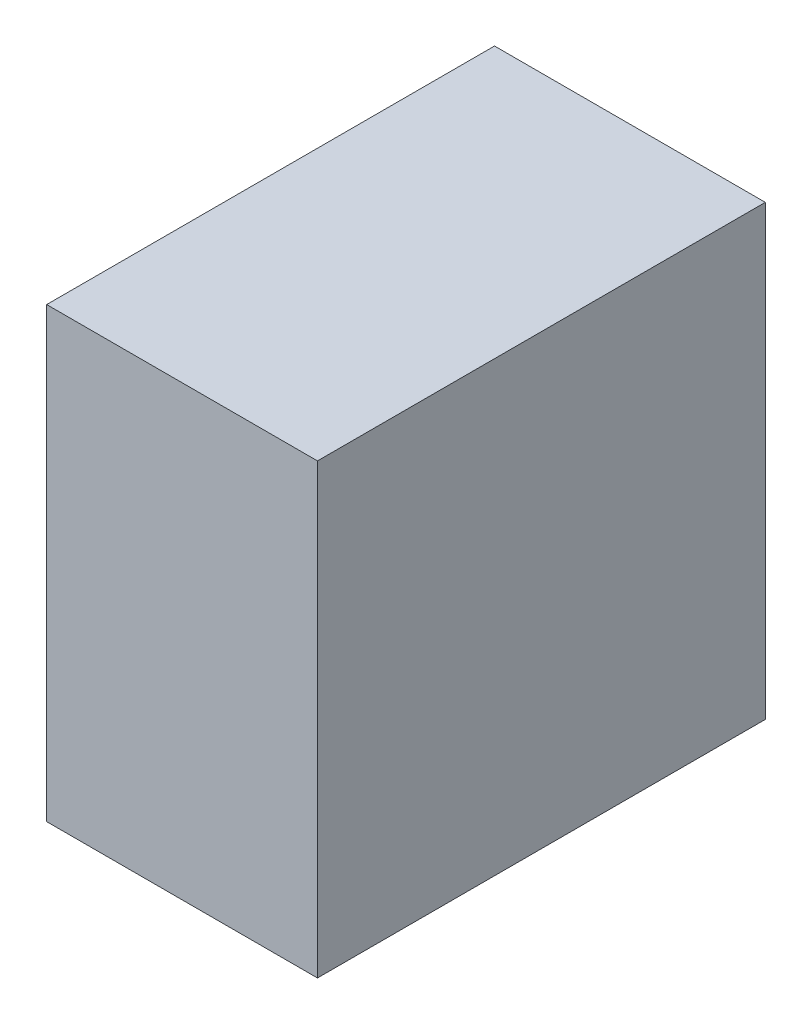
SolidWorks part; units mm, degrees
ref_plane "Ön Düzlem" through (0, 0, 0) normal (0, 0, 1) x (1, 0, 0)
ref_plane "Üst Düzlem" through (0, 0, 0) normal (0, 1, 0) x (1, 0, 0)
ref_plane "Sağ Düzlem" through (0, 0, 0) normal (1, 0, 0) x (0, 0, -1)
sketch "Sketch1" plane through (0, 0, 0) normal (0, 0, 1) x (1, 0, 0)
  line L1 (-13, 21.5) -> (13, 21.5)
  line L2 (-13, 21.5) -> (-13, -21.5)
  line L3 (-13, -21.5) -> (13, -21.5)
  line L4 (13, 21.5) -> (13, -21.5)
  line L5 (-13, 21.5) -> (13, -21.5) construction
  line L6 (-13, -21.5) -> (13, 21.5) construction
  point P0 (0, 0)
  dimension "D1" = 43
  dimension "D2" = 26
extrude "Boss-Extrude1" add sketch "Sketch1" along normal blind 43
